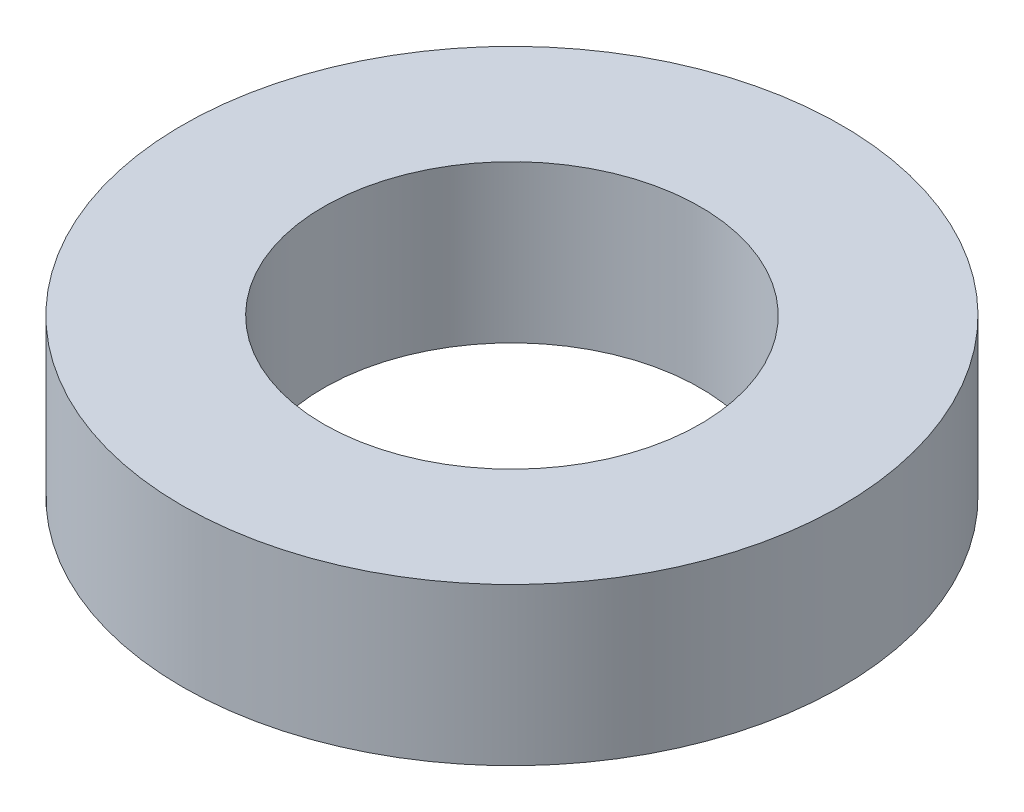
SolidWorks part; units mm, degrees
ref_plane "Front Plane" through (0, 0, 0) normal (0, 0, 1) x (1, 0, 0)
ref_plane "Top Plane" through (0, 0, 0) normal (0, 1, 0) x (1, 0, 0)
ref_plane "Right Plane" through (0, 0, 0) normal (1, 0, 0) x (0, 0, -1)
sketch "Sketch5" plane through (0, 0, 0) normal (0, 1, 0) x (1, 0, 0)
  circle A0 centre (0, 0) radius 10.5
  dimension "D1" = 21
extrude "Boss-Extrude2" add sketch "Sketch5" along normal blind 5
sketch "Sketch6" plane through (0, 5, 0) normal (0, 1, 0) x (1, 0, 0)
  circle A0 centre (0, 0) radius 6
  dimension "D1" = 12
extrude "Cut-Extrude3" cut sketch "Sketch6" against normal blind 8
